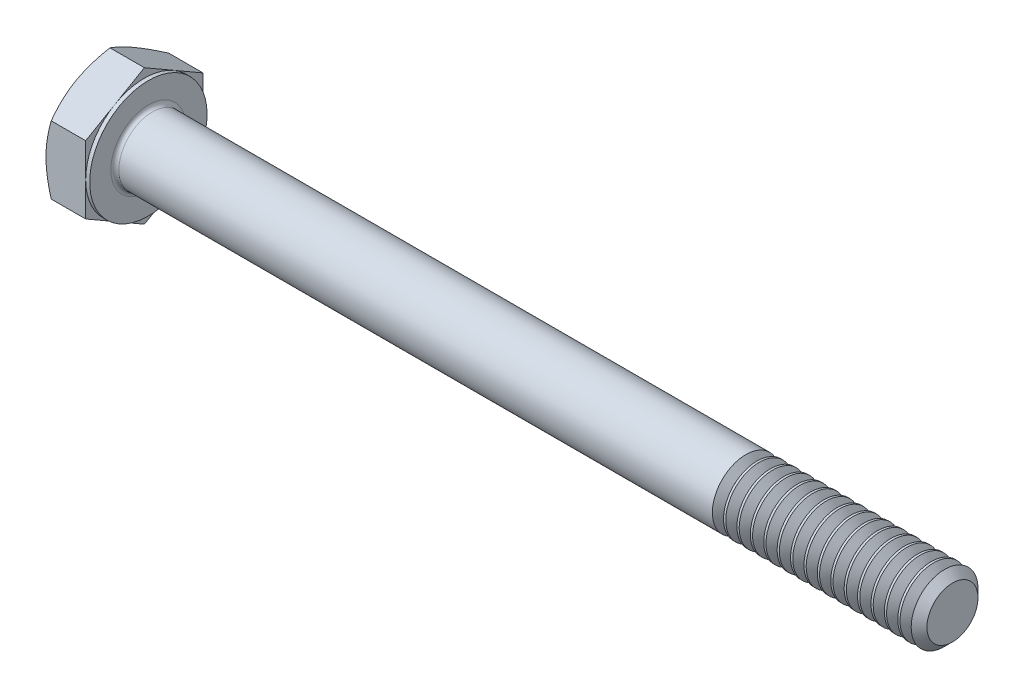
SolidWorks part; units mm, degrees
extrude "BaseHead" add sketch "Sketch1" along normal blind 4.1402
sketch "Sketch1" plane through (0, 0, 0) normal (1, 0, 0) x (0, 0, -1)
  line L0 (5.5626, 3.2116) -> (5.5626, -3.2116)
  line L1 (-5.5626, 3.2116) -> (-5.5626, -3.2116)
  line L2 (5.5626, -3.2116) -> (0, -6.4231)
  line L3 (0, -6.4231) -> (-5.5626, -3.2116)
  line L4 (5.5626, 3.2116) -> (0, 6.4231)
  line L5 (0, 6.4231) -> (-5.5626, 3.2116)
  dimension "Width_flats" = 11.1252
  dimension "D2" = 120
  dimension "D3" = 5.5626
  dimension "D4" = 5.5626
  dimension "D5" = 5.5626
revolve "HeadChamfer" cut sketch "Sketch3" angle 360 about L6
sketch "Sketch3" plane through (0, 0, 0) normal (0, 0, 1) x (1, 0, 0)
  line L0 (0, 5.5626) -> (4.163, 12.7731)
  line L1 (0, 6.4231) -> (0, 3.2116) construction
  line L2 (4.163, 12.7731) -> (4.163, 19.1231)
  line L3 (4.163, 19.1231) -> (-12.7, 19.1231)
  line L4 (-12.7, 19.1231) -> (-12.7, 5.5626)
  line L5 (-12.7, 5.5626) -> (0, 5.5626)
  line L6 (0, 0) -> (99.06, 0) construction
  line L7 (4.1402, 6.4231) -> (0, 6.4231) construction
  dimension "D1" = 5.5626
  dimension "D2" = 6.35
  dimension "D3" = 12.7
  dimension "D4" = 6.35
  dimension "Head_ch_ang" = 30
ref_plane "Plane1" through (0, 0, 0) normal (0, 0, 1) x (1, 0, 0)
ref_plane "Plane2" through (0, 0, 0) normal (0, 1, 0) x (1, 0, 0)
ref_plane "Plane3" through (0, 0, 0) normal (1, 0, 0) x (0, 0, -1)
sketch "BodySke" plane through (0, 0, 0) normal (0, 0, 1) x (1, 0, 0)
  line L0 (0, 3.2116) -> (0, -3.2116) construction
  line L1 (0, 0) -> (80.3402, 0)
  line L2 (0, 0) -> (0, 3.175)
  line L3 (0, 3.175) -> (79.5845, 3.175)
  line L4 (80.3402, 0) -> (80.3402, 2.4193)
  line L5 (4.1402, 6.4231) -> (4.1402, 3.2116) construction
  line L6 (80.3402, 2.4193) -> (79.5845, 3.175)
  line L7 (0, 0) -> (96.52, 0) construction
  line L8 (80.3402, -2.4193) -> (79.5845, -3.175) construction
  line L9 (0, -3.175) -> (79.5845, -3.175) construction
  line L10 (5.4102, 15.24) -> (5.4102, -1.27) construction
  line L11 (61.2902, 15.24) -> (61.2902, -1.27) construction
  line L12 (4.1402, 3.2116) -> (4.1402, -3.2116) construction
  dimension "Diameter" = 6.35
revolve "BaseBody" add sketch "BodySke" angle 360 about L7
cosmetic thread "ThreadCosmetic" [suppressed] parameters "Thread_length"=19.05, "Thread_minor"=4.8387
sketch "Sketch4" plane through (0, 0, 0) normal (0, 0, 1) x (1, 0, 0)
  line L1 (4.1402, 6.4231) -> (4.1402, 3.2116) construction
  line L2 (4.1402, 5.5626) -> (3.7592, 5.5626)
  line L3 (4.1402, 5.5626) -> (4.1402, 31.8231)
  line L4 (4.1402, 31.8231) -> (3.7592, 31.8231)
  line L5 (0, 0) -> (95.25, 0) construction
  line L6 (0, 0) -> (96.52, 0) construction
  line L7 (3.7592, 5.5626) -> (3.7592, 31.8231)
  line L8 (4.1402, 6.4231) -> (0.4968, 6.4231) construction
  dimension "D1" = 5.5626
  dimension "D2" = 25.4
revolve "BearingFace" cut sketch "Sketch4" angle 360 about L5
fillet "HeadFillet" radius 0.381 1 edges at (4.1402, 0, -3.175)
sketch "ThdSchSke" plane through (0, 0, 0) normal (0, 0, 1) x (1, 0, 0)
  line L0 (61.2902, -2.4193) -> (60.7611, -3.175)
  line L1 (61.2902, -2.4193) -> (61.8193, -3.175)
  line L2 (61.8193, -3.175) -> (61.8193, -3.9687)
  line L3 (-3.175, 0) -> (5.1513, 0) construction
  line L5 (61.8193, -3.9687) -> (60.7611, -3.9687)
  line L6 (60.7611, -3.9687) -> (60.7611, -3.175)
  dimension "Thread_minor" = 4.8387
  dimension "Diameter" = 6.35
  dimension "Start" = 61.2902
revolve "ThreadSchematic" cut sketch "ThdSchSke" angle 360 about L3
pattern_linear "ThdSchPat" count 15 spacing 1.27 along (1, 0, 0) of "ThreadSchematic"
equation "\"D3@Sketch1\" = \"Width_flats@Sketch1\" / 2"
equation "\"D4@Sketch1\" = \"D3@Sketch1\""
equation "\"D5@Sketch1\" = \"D4@Sketch1\""
equation "\"Thread_minor@ThreadCosmetic\" = \"Minor_dia@BodySke\""
equation "\"D1@Sketch3\" = \"Width_flats@Sketch1\" / 2"
equation "\"D1@Sketch4\" = \"Width_flats@Sketch1\" / 2"
equation "\"Thread_length@ThreadCosmetic\" = ((sgn( (\"Length@BodySke\" - \"Advance@BodySke\" ) - \"Thread_nom@BodySke\" )-1)*( (\"Length@BodySke\" - \"Advance@BodySke\" ) - \"Thread_nom@BodySke\" ))/-2+ \"Thread_nom@BodySke\""
equation "\"Thread_minor@ThdSchSke\" = \"Minor_dia@BodySke\""
equation "\"Diameter@ThdSchSke\" = \"Diameter@BodySke\""
equation "\"Overcut@ThdSchSke\" = \"Diameter@BodySke\" * 1.25"
equation "\"Start@ThdSchSke\" = \"Head_ht@BaseHead\" + \"Length@BodySke\" - \"Thread_length@ThreadCosmetic\"  '---Non-countersunk---"
equation "\"Num_threads@ThdSchPat\" = int( \"Thread_length@ThreadCosmetic\" / \"Advance@BodySke\" + 0.999 )  + 1"
equation "\"Advance@ThdSchPat\" = \"Thread_length@ThreadCosmetic\" /  (\"Num_threads@ThdSchPat\" - 1) 'relax it"
equation "\"Num_threads@ThdSchPat\" = \"Num_threads@ThdSchPat\" - sgn( \"Num_threads@ThdSchPat\" - 1) '---chamfered tips only---"
